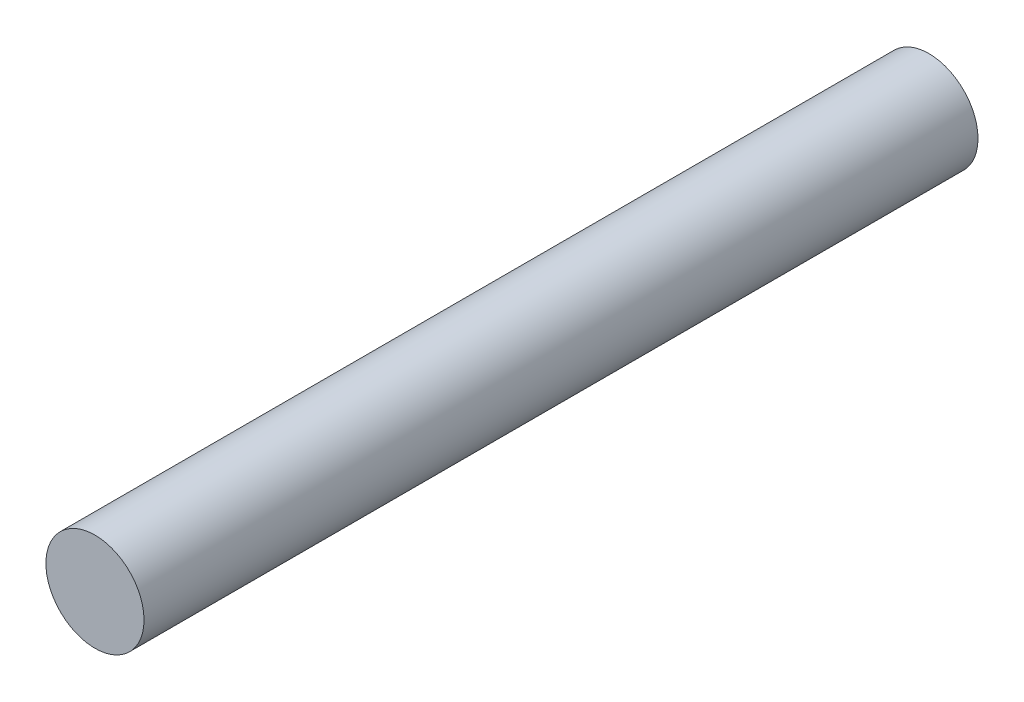
SolidWorks part; units mm, degrees
ref_plane "Front Plane" through (0, 0, 0) normal (0, 0, 1) x (1, 0, 0)
ref_plane "Top Plane" through (0, 0, 0) normal (0, 1, 0) x (1, 0, 0)
ref_plane "Right Plane" through (0, 0, 0) normal (1, 0, 0) x (0, 0, -1)
sketch "Sketch1" plane through (0, 0, 0) normal (0, 0, 1) x (1, 0, 0)
  circle A0 centre (0, 0) radius 2.5
  dimension "D1" = 5
extrude "Boss-Extrude1" add sketch "Sketch1" along normal blind 42.5
